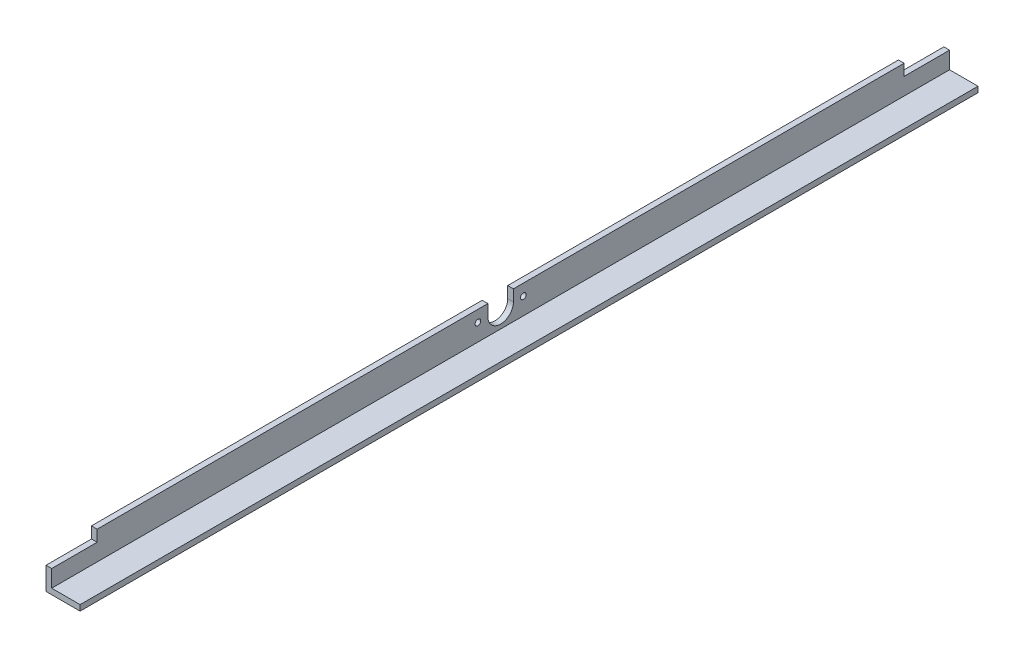
SolidWorks part; units mm, degrees
ref_plane "Front Plane" through (0, 0, 0) normal (0, 0, 1) x (1, 0, 0)
ref_plane "Top Plane" through (0, 0, 0) normal (0, 1, 0) x (1, 0, 0)
ref_plane "Right Plane" through (0, 0, 0) normal (1, 0, 0) x (0, 0, -1)
sketch "Sketch1" plane through (0, 0, 0) normal (0, 0, 1) x (1, 0, 0)
  line L0 (0, 0) -> (0, 38.1)
  line L1 (0, 38.1) -> (6.35, 38.1)
  line L2 (6.35, 38.1) -> (6.35, 6.35)
  line L3 (6.35, 6.35) -> (0, 0) construction
  line L4 (38.1, 6.35) -> (6.35, 6.35)
  line L5 (38.1, 0) -> (38.1, 6.35)
  line L6 (0, 0) -> (38.1, 0)
  dimension "D1" = 45
  dimension "D2" = 38.1
  dimension "D3" = 6.35
extrude "Boss-Extrude1" add sketch "Sketch1" along normal blind 1003.3
sketch "Sketch2" plane through (6.35, 0, 0) normal (1, 0, 0) x (0, 0, -1)
  line L0 (-501.65, 0) -> (-501.65, 25.4) construction
  line L3 (-1003.3, 0) -> (0, 0) construction
  line L4 (-515.9375, 25.4) -> (-515.9375, 38.1)
  line L5 (-1003.3, 38.1) -> (0, 38.1) construction
  line L6 (-487.3625, 25.4) -> (-487.3625, 38.1)
  line L7 (-487.3625, 38.1) -> (-487.3625, 50.2994)
  line L8 (-487.3625, 50.2994) -> (-515.9375, 50.2994)
  line L9 (-515.9375, 50.2994) -> (-515.9375, 38.1)
  line L10 (-501.65, 25.4) -> (-527.05, 25.4) construction
  line L11 (-527.05, 25.4) -> (-527.05, 38.1) construction
  circle A0 centre (-501.65, 25.4) radius 14.2875
  circle A1 centre (-527.05, 25.4) radius 3.175
  circle A2 centre (-476.25, 25.4) radius 3.175
  dimension "D1" = 28.575
  dimension "D5" = 6.35
  dimension "D2" = 25.4
  dimension "D3" = 25.4
  dimension "D4" = 12.7
extrude "Cut-Extrude1" cut sketch "Sketch2" against normal up to next
sketch "Sketch3" plane through (6.35, 0, 0) normal (1, 0, 0) x (0, 0, -1)
  line L0 (-501.65, 11.1125) -> (-501.65, 140.9513) construction
  line L1 (0, 38.1) -> (-50.8, 38.1)
  line L2 (0, 38.1) -> (0, 25.4)
  line L3 (0, 25.4) -> (-50.8, 25.4)
  line L4 (-50.8, 38.1) -> (-50.8, 25.4)
  line L5 (-952.5, 38.1) -> (-952.5, 25.4)
  line L6 (-1003.3, 25.4) -> (-952.5, 25.4)
  line L7 (-1003.3, 38.1) -> (-1003.3, 25.4)
  line L8 (-1003.3, 38.1) -> (-952.5, 38.1)
  arc A0 (-515.9375, 25.4) -> (-487.3625, 25.4) centre (-501.65, 25.4) ccw construction
  dimension "D1" = 12.7
  dimension "D2" = 50.8
extrude "Cut-Extrude2" cut sketch "Sketch3" against normal through all
